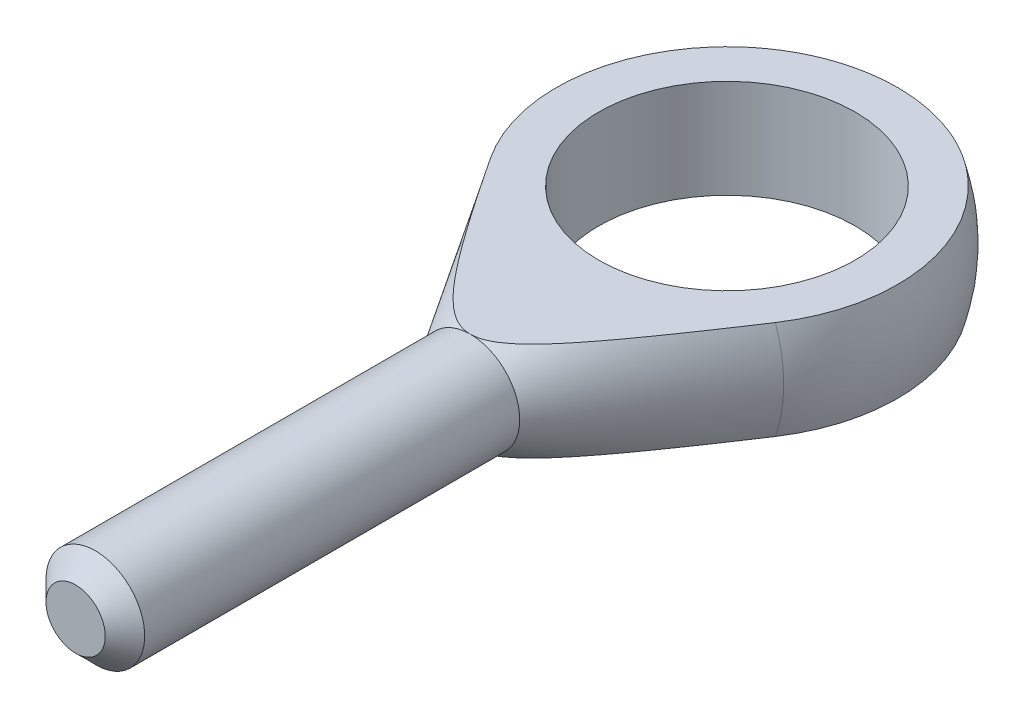
SolidWorks part; units mm, degrees
material "1.0545 (S355N)"
ref_plane "Płaszczyzna przednia" through (0, 0, 0) normal (0, 0, 1) x (1, 0, 0)
ref_plane "Płaszczyzna górna" through (0, 0, 0) normal (0, 1, 0) x (1, 0, 0)
ref_plane "Płaszczyzna prawa" through (0, 0, 0) normal (1, 0, 0) x (0, 0, -1)
sketch "Szkic1" plane through (0, 0, 0) normal (0, 1, 0) x (1, 0, 0)
  line L0 (0, 26.0435) -> (0, -71.4286) construction
  line L1 (-2.5, -33) -> (2.5, -33)
  line L2 (2.5, -33) -> (2.5, -13)
  line L3 (-2.5, -33) -> (-2.5, -13)
  line L4 (-7.6369, -4.7621) -> (-2.5, -13)
  line L5 (2.5, -13) -> (7.6369, -4.7621)
  line L6 (-2.5, -13) -> (2.5, -13)
  line L7 (0, 9) -> (0, -33)
  arc A0 (7.6369, -4.7621) -> (-7.6369, -4.7621) centre (0, 0) ccw
  point P7 (0, -33)
  dimension "d4" = 18
  dimension "d2" = 5
  dimension "l1" = 33
  dimension "l3" = 20
revolve "Obrót1" add sketch "Szkic1" angle 360 about L0
sketch "Szkic2" plane through (0, 0, 0) normal (1, 0, 0) x (0, 0, -1)
  line L4 (-13, 2.5) -> (8.6458, 2.5)
  line L5 (-13, -2.5) -> (8.6458, -2.5)
  line L6 (-13, -2.5) -> (-4.7621, -7.6369) construction
  line L7 (-4.7621, 7.6369) -> (-13, 2.5) construction
  line L8 (-13, -2.5) -> (-4.7621, -7.6369)
  line L9 (-4.7621, 7.6369) -> (-13, 2.5)
  arc A0 (-4.7621, -7.6369) -> (-4.7621, 7.6369) centre (0, 0) ccw construction
  arc A1 (-4.7621, -7.6369) -> (8.6458, -2.5) centre (0, 0) ccw
  arc A2 (8.6458, 2.5) -> (-4.7621, 7.6369) centre (0, 0) ccw
extrude "Wytnij-wyciągnięcie1" cut sketch "Szkic2" against normal through all both and the other way through all
sketch "Szkic3" plane through (0, 0, 0) normal (0, 1, 0) x (1, 0, 0)
  circle A0 centre (0, 0) radius 6.5
  dimension "b" = 13
extrude "Wytnij-wyciągnięcie2" cut sketch "Szkic3" against normal through all both and the other way through all contours A0
chamfer "Sfazowanie1" distance 1 angle 45 1 edges at (-2.5, 0, 33)
equation "\"D1@Sfazowanie1\"=\"l3@Szkic1\"*0.05"
